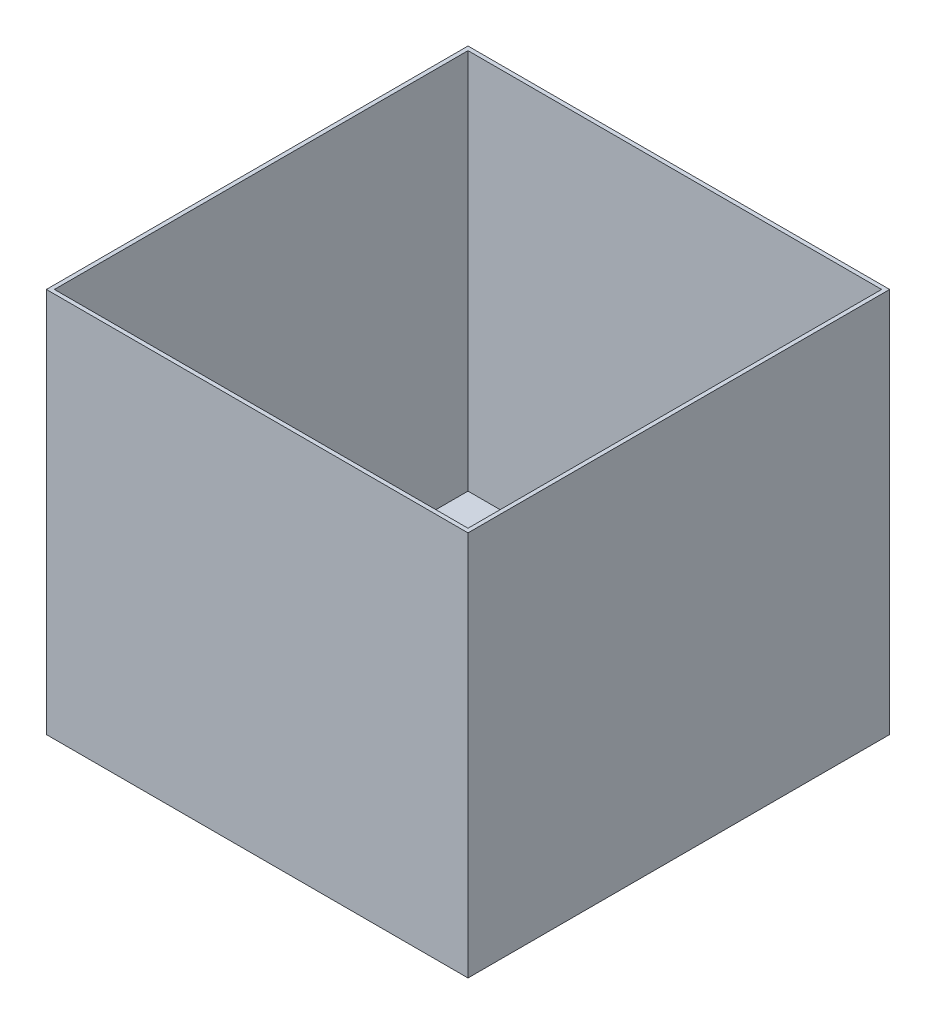
SolidWorks part; units mm, degrees
ref_plane "Front Plane" through (0, 0, 0) normal (0, 0, 1) x (1, 0, 0)
ref_plane "Top Plane" through (0, 0, 0) normal (0, 1, 0) x (1, 0, 0)
ref_plane "Right Plane" through (0, 0, 0) normal (1, 0, 0) x (0, 0, -1)
sketch "Sketch1" plane through (0, 0, 0) normal (0, 0, 1) x (1, 0, 0)
  line L1 (105, 96) -> (-105, 96)
  line L2 (105, 96) -> (105, -96)
  line L3 (105, -96) -> (-105, -96)
  line L4 (-105, 96) -> (-105, -96)
  line L5 (105, 96) -> (-105, -96) construction
  line L6 (105, -96) -> (-105, 96) construction
  point P0 (0, 0)
  dimension "D1" = 210
  dimension "D2" = 192
extrude "Boss-Extrude1" add sketch "Sketch1" along normal mid plane 210
sketch "Sketch2" plane through (0, 96, 0) normal (0, 1, 0) x (1, 0, 0)
  line L12 (103, 103) -> (-103, 103)
  line L13 (-103, 103) -> (-103, -103)
  line L14 (-103, -103) -> (103, -103)
  line L15 (103, -103) -> (103, 103)
  line L16 (103, 103) -> (-103, 103)
  line L17 (-103, 103) -> (-103, -103)
  line L18 (-103, -103) -> (103, -103)
  line L19 (103, -103) -> (103, 103)
  dimension "D1" = 2
extrude "Cut-Extrude1" cut sketch "Sketch2" against normal offset from surface (190 mm away) 2 up to face at (0, -96, 0)
